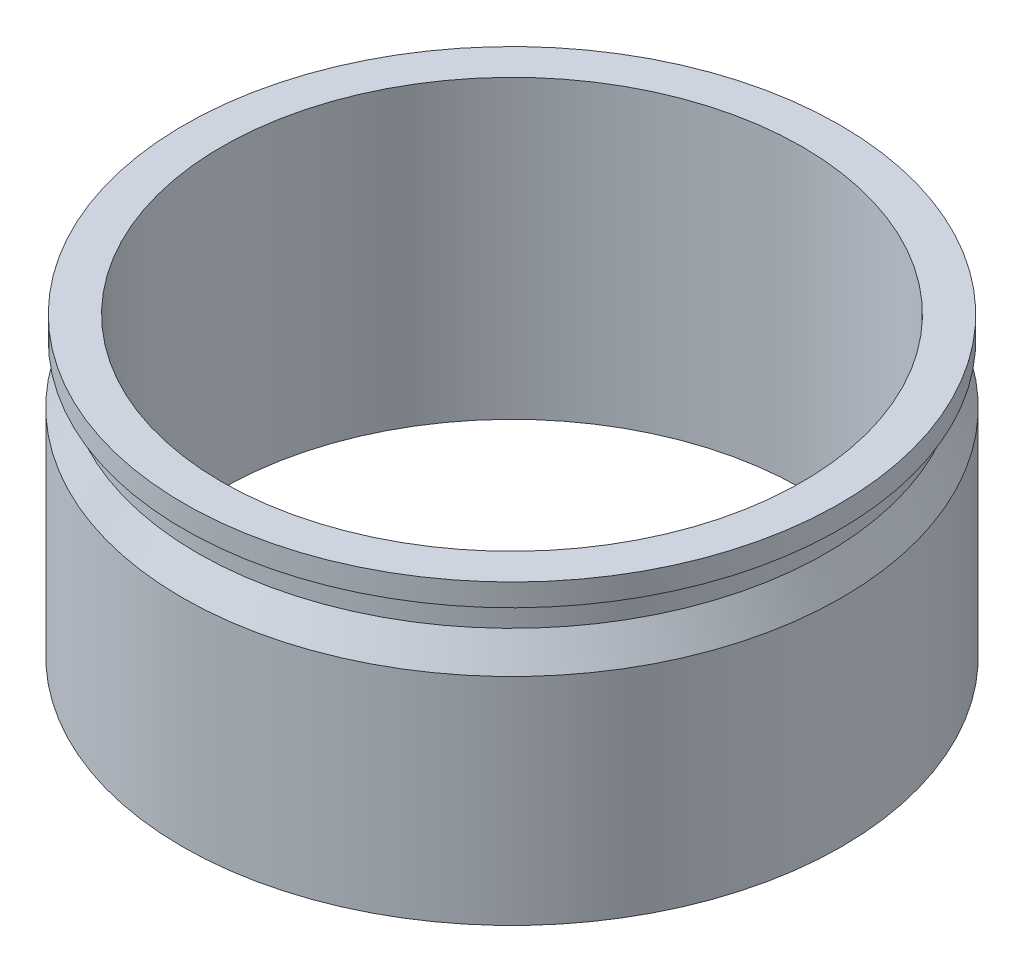
SolidWorks part; units mm, degrees
ref_plane "Front Plane" through (0, 0, 0) normal (0, 0, 1) x (1, 0, 0)
ref_plane "Top Plane" through (0, 0, 0) normal (0, 1, 0) x (1, 0, 0)
ref_plane "Right Plane" through (0, 0, 0) normal (1, 0, 0) x (0, 0, -1)
sketch "Sketch2" plane through (0, 0, 0) normal (0, 0, 1) x (1, 0, 0)
  line L0 (-368.75, 1708.8376) -> (-326.5, 1708.8376) construction
  line L1 (-368.75, 1949.4) -> (-368.75, 1708.8376) construction
  line L2 (-351.5, 1984) -> (-368.75, 1949.4) construction
  line L3 (-351.5, 2016) -> (-351.5, 1984) construction
  line L4 (-366.75, 2016) -> (-351.5, 2016) construction
  line L5 (-366.75, 2039) -> (-366.75, 2016) construction
  line L6 (-326.5, 2039) -> (-366.75, 2039) construction
  line L7 (-326.5, 1708.8376) -> (-326.5, 2039) construction
  line L8 (-368.75, 1708.8376) -> (-326.5, 1708.8376)
  line L9 (-368.75, 1949.4) -> (-368.75, 1708.8376)
  line L10 (-351.5, 1984) -> (-368.75, 1949.4)
  line L11 (-351.5, 2016) -> (-351.5, 1984)
  line L12 (-366.75, 2016) -> (-351.5, 2016)
  line L13 (-366.75, 2039) -> (-366.75, 2016)
  line L14 (-326.5, 2039) -> (-366.75, 2039)
  line L15 (-326.5, 1708.8376) -> (-326.5, 2039)
  line L16 (0, 1764) -> (0, 2710.9154) construction
  line L17 (0, 1764) -> (0, 2710.9154)
revolve "Revolve-Thin1" add sketch "Sketch2" angle 360 about L17
